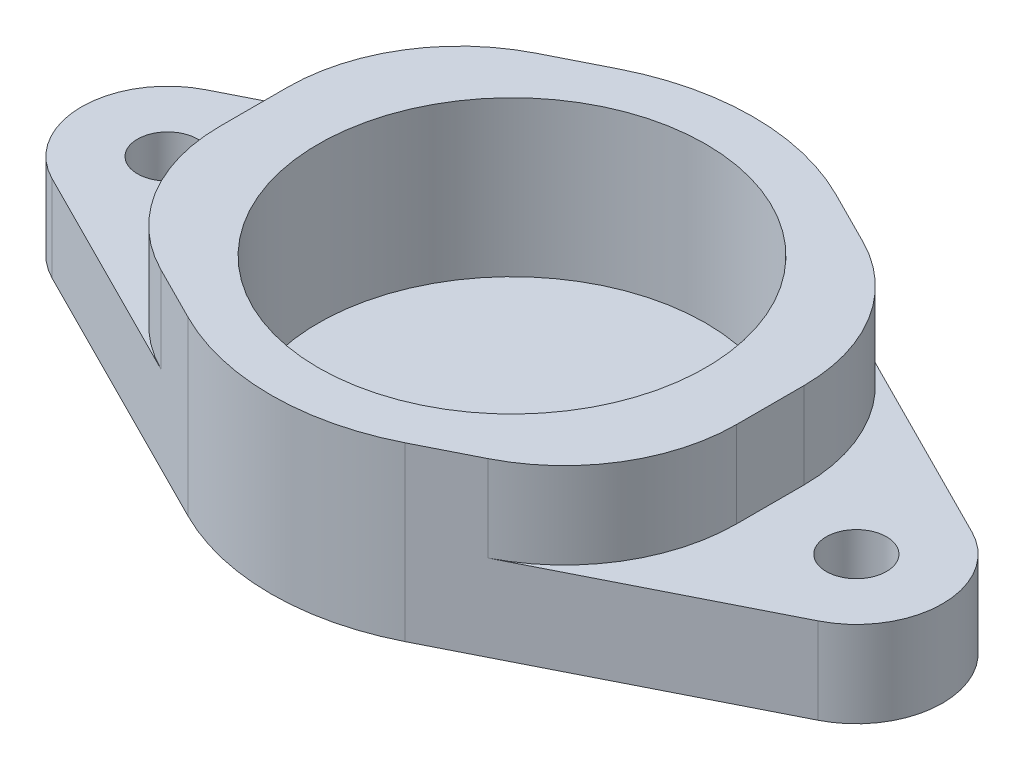
SolidWorks part; units mm, degrees
ref_plane "Front Plane" through (0, 0, 0) normal (0, 0, 1) x (1, 0, 0)
ref_plane "Top Plane" through (0, 0, 0) normal (0, 1, 0) x (1, 0, 0)
ref_plane "Right Plane" through (0, 0, 0) normal (1, 0, 0) x (0, 0, -1)
sketch "Sketch2" plane through (0, 0, 0) normal (0, 1, 0) x (1, 0, 0)
  line L0 (-22.25, 4.4651) -> (-6.3, 12.5024)
  line L1 (6.3, 12.5024) -> (22.25, 4.4651)
  line L2 (-22.25, -4.4651) -> (-6.3, -12.5024)
  line L3 (6.3, -12.5024) -> (22.25, -4.4651)
  arc A0 (6.3, 12.5024) -> (-6.3, 12.5024) centre (0, 0) ccw
  arc A1 (-22.25, 4.4651) -> (-22.25, -4.4651) centre (-20, 0) ccw
  arc A2 (22.25, -4.4651) -> (22.25, 4.4651) centre (20, 0) ccw
  circle A4 centre (-20, 0) radius 1.75
  circle A5 centre (20, 0) radius 1.75
  arc A6 (-6.3, -12.5024) -> (6.3, -12.5024) centre (0, 0) ccw
  dimension "D1" = 28
  dimension "D2" = 10
  dimension "D3" = 10
  dimension "D4" = 3.5
  dimension "D5" = 3.5
  dimension "D6" = 20
  dimension "D7" = 20
extrude "Boss-Extrude1" add sketch "Sketch2" along normal blind 10
sketch "Sketch3" plane through (0, 10, 0) normal (0, 1, 0) x (1, 0, 0)
  circle A0 centre (0, 0) radius 11.25
extrude "Cut-Extrude1" cut sketch "Sketch3" against normal blind 9
sketch "Sketch4" plane through (0, 0, 0) normal (0, 0, 1) x (1, 0, 0)
  line L0 (-22.25, 10) -> (-6.3, 10) construction
  line L1 (-15, 10) -> (-25, 10)
  line L2 (-15, 10) -> (-15, 5)
  line L3 (-15, 5) -> (-25, 5)
  line L4 (-25, 10) -> (-25, 5)
  line L5 (-25, 10) -> (-25, 0) construction
  line L6 (6.3, 10) -> (22.25, 10) construction
  line L7 (15, 10) -> (25, 10)
  line L8 (15, 10) -> (15, 5)
  line L9 (15, 5) -> (25, 5)
  line L10 (25, 10) -> (25, 5)
  line L11 (25, 0) -> (25, 10) construction
  line L12 (-22.25, 0) -> (-6.3, 0) construction
  line L13 (18.25, 0) -> (21.75, 0) construction
  dimension "D1" = 10
  dimension "D2" = 10
  dimension "D3" = 5
  dimension "D4" = 5
extrude "Cut-Extrude2" cut sketch "Sketch4" against normal through all both and the other way through all
fillet "Fillet1" radius 10 4 edges at (15, 7.5, 8.1184) (15, 7.5, -8.1184) (-15, 7.5, -8.1184) (-15, 7.5, 8.1184)
